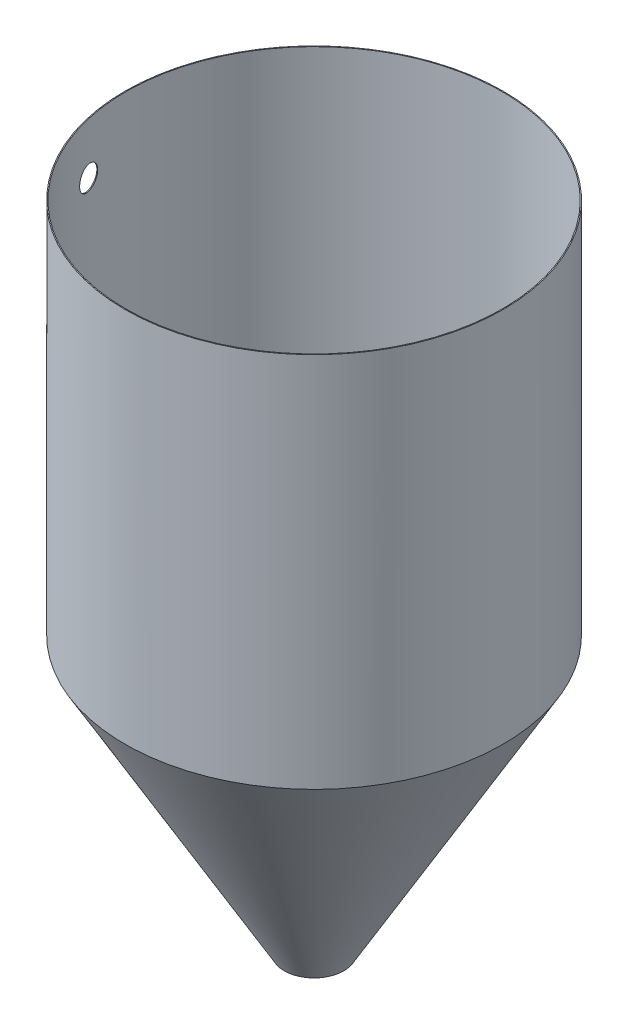
SolidWorks part; units mm, degrees
material "5052-H36"
ref_plane "Front Plane" through (0, 0, 0) normal (0, 0, 1) x (1, 0, 0)
ref_plane "Top Plane" through (0, 0, 0) normal (0, 1, 0) x (1, 0, 0)
ref_plane "Right Plane" through (0, 0, 0) normal (1, 0, 0) x (0, 0, -1)
sketch "Sketch1" plane through (0, 0, 0) normal (0, 1, 0) x (1, 0, 0)
  circle A0 centre (0, 0) radius 254
  circle A1 centre (0, 0) radius 255.2141
  dimension "D1" = 508
  dimension "D2" = 1.2141
extrude "Boss-Extrude1" add sketch "Sketch1" along normal blind 508
sketch "Sketch2" plane through (0, 0, 0) normal (0, 0, 1) x (1, 0, 0)
  line L0 (254, 0) -> (38.989, -372.41)
  line L1 (254, 0) -> (0, -439.9409) construction
  line L2 (0, -439.9409) -> (0, 0) construction
  line L3 (254, 0) -> (-254, 0) construction
  line L4 (38.989, -372.41) -> (40.2031, -372.41)
  line L5 (40.2031, -372.41) -> (255.2141, 0)
  line L6 (255.2141, 0) -> (254, 0)
  line L7 (254, 0) -> (254, 508) construction
  dimension "D1" = 77.978
  dimension "D2" = 508
  dimension "D3" = 508
revolve "Revolve1" add sketch "Sketch2" angle 360 about L2
sketch "Sketch3" plane through (0, 53.975, 0) normal (1, 0, 0) x (0, 0, -1)
  circle A0 centre (-57.15, 384.9808) radius 15.875
  dimension "D1" = 31.75
extrude "Cut-Extrude1" cut sketch "Sketch3" against normal blind 304.8
equation "\"D3@Sketch2\"=\"D2@Sketch2\""
